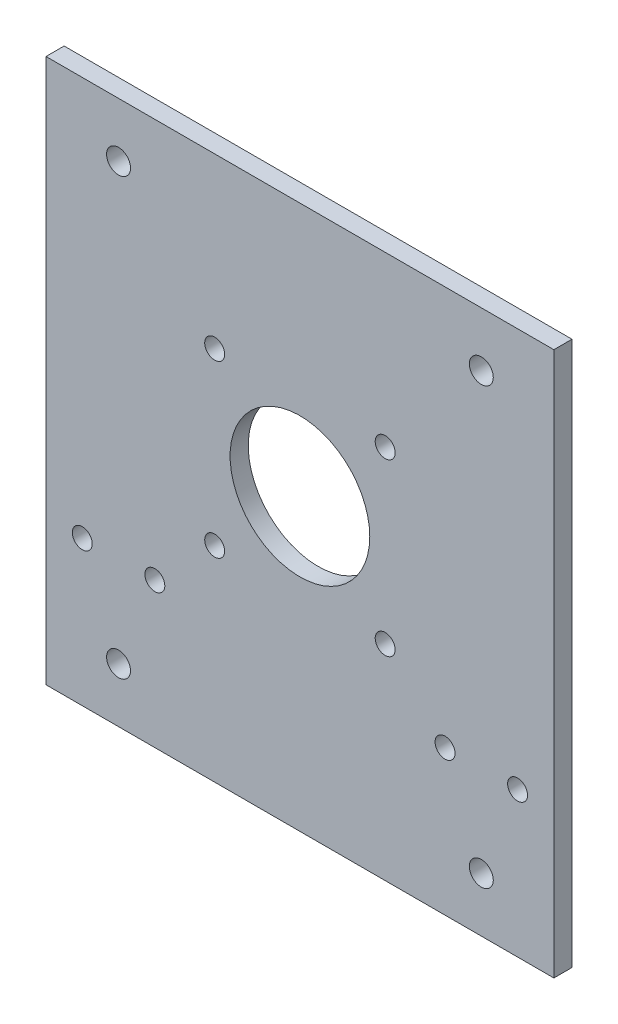
SolidWorks part; units mm, degrees
material "6061 Alloy"
ref_plane "Front Plane" through (0, 0, 0) normal (0, 0, 1) x (1, 0, 0)
ref_plane "Top Plane" through (0, 0, 0) normal (0, 1, 0) x (1, 0, 0)
ref_plane "Right Plane" through (0, 0, 0) normal (1, 0, 0) x (0, 0, -1)
sketch "Sketch1" plane through (0, 0, 0) normal (0, 0, 1) x (1, 0, 0)
  line L1 (-70, -86) -> (70, -86)
  line L2 (-70, -86) -> (-70, 64)
  line L3 (-70, 64) -> (70, 64)
  line L4 (70, -86) -> (70, 64)
  line L5 (-70, -86) -> (70, 64) construction
  line L6 (-70, 64) -> (70, -86) construction
  circle A0 centre (23.5, 17.5) radius 2.75
  circle A1 centre (-23.5, 17.5) radius 2.75
  circle A2 centre (-23.5, -29.5) radius 2.75
  circle A3 centre (23.5, -29.5) radius 2.75
  circle A4 centre (0, -6) radius 19.25
  point P0 (0, 0)
  point P18 (0, -11)
  dimension "D3" = 5.5
  dimension "D7" = 38.5
  dimension "D9" = 23.5
  dimension "D4" = 5
  dimension "D1" = 140
  dimension "D2" = 150
  dimension "D5" = 2
  dimension "D8" = 23.5
  dimension "D6" = 2
extrude "Boss-Extrude1" add sketch "Sketch1" along normal blind 5
sketch "Sketch2" plane through (0, 0, 0) normal (0, 0, -1) x (-1, 0, 0)
  line L0 (60, -46) -> (-60, -46)
  line L2 (-70, -86) -> (-70, 64) construction
  point P3 (40, -46)
  point P6 (-40, -46)
  dimension "D1" = 120
  dimension "D2" = 46
  dimension "D3" = 10
  dimension "D4" = 20
  dimension "D5" = 20
hole_wizard "Ø5.0mm Dowel Hole1" positions "3DSketch1" profile "Sketch4" hole size "Ø5.0" standard "ISO" end condition through all
sketch3d "3DSketch1"
  point P0 (60, -46, 0)
  point P3 (-60, -46, 0)
  point P7 (-40, -46, 0)
  point P10 (40, -46, 0)
sketch "Sketch4" plane through (60, -46, 0) normal (1, 0, 0) x (0, 1, 0)
  line L0 (0, 0) -> (0, 5)
  line L1 (0, 5) -> (2.75, 5)
  line L2 (2.75, 5) -> (2.75, 0)
  line L5 (2.75, 0) -> (0, 0)
  line L11 (0, -6.35) -> (0, 107.95) construction
  dimension "Thru Hole Dia." = 5.5
  dimension "Thru Hole Depth" = 5
sketch "Sketch5" plane through (0, 0, 5) normal (0, 0, 1) x (1, 0, 0)
  line L0 (-70, 64) -> (-70, -86) construction
  line L1 (70, 64) -> (-70, 64) construction
  circle A0 centre (-50, 49) radius 3.1796
  circle A1 centre (50, 49) radius 3.1796
  circle A2 centre (50, -71) radius 3.1796
  circle A3 centre (-50, -71) radius 3.1796
  dimension "D2" = 15
  dimension "D1" = 20
  dimension "D3" = 2
  dimension "D4" = 2
hole_wizard "Ø6.0mm Dowel Hole2" positions "3DSketch2" profile "Sketch7" hole size "Ø6.0" standard "ISO"
sketch3d "3DSketch2"
  point P0 (-50, 49, 5)
  point P3 (50, 49, 5)
  point P6 (50, -71, 5)
  point P9 (-50, -71, 5)
sketch "Sketch7" plane through (-50, 49, 5) normal (1, 0, 0) x (0, -1, 0)
  line L0 (0, 0) -> (0, 6.9818)
  line L1 (0, 6.9818) -> (3.3, 4.999)
  line L2 (3.3, 4.999) -> (3.3, 0)
  line L5 (3.3, 0) -> (0, 0)
  line L10 (0, 6.9818) -> (-3.3, 4.999) construction
  line L11 (0, -6.35) -> (0, 107.95) construction
  dimension "Hole Dia." = 6.6
  dimension "Hole Depth" = 4.999
  dimension "Drill Angle" = 118
